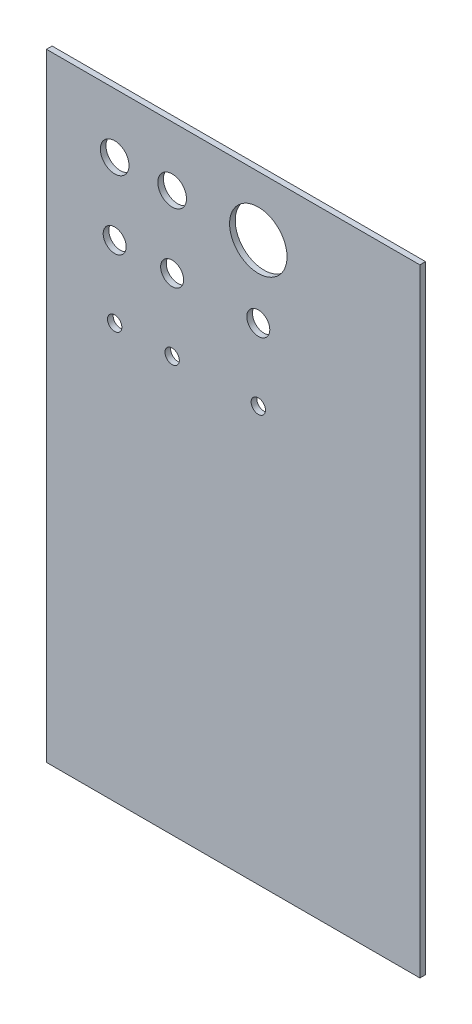
SolidWorks part; units mm, degrees
ref_plane "Front Plane" through (0, 0, 0) normal (0, 0, 1) x (1, 0, 0)
ref_plane "Top Plane" through (0, 0, 0) normal (0, 1, 0) x (1, 0, 0)
ref_plane "Right Plane" through (0, 0, 0) normal (1, 0, 0) x (0, 0, -1)
sketch "Sketch1" plane through (0, 0, 0) normal (0, 0, 1) x (1, 0, 0)
  circle B0 centre (1873.254, 4935.2365) radius 254
  line B1 (3302, 5461) -> (3302, 0)
  line B2 (0, 0) -> (0, 5461)
  line B3 (0, 5461) -> (3302, 5461)
  line B4 (3302, 0) -> (0, 0)
  circle B5 centre (603.254, 4935.2365) radius 127
  circle B6 centre (603.254, 4300.2365) radius 101.6
  circle B7 centre (603.254, 3665.2365) radius 63.5
  circle B8 centre (1111.254, 4935.2365) radius 127
  circle B9 centre (1111.254, 4300.2365) radius 101.6
  circle B10 centre (1111.254, 3665.2365) radius 63.5
  circle B11 centre (1873.254, 4300.2365) radius 101.6
  circle B12 centre (1873.254, 3665.2365) radius 63.5
sketch_block_instance "support-1"
sketch_block "support"
extrude "Boss-Extrude1" add sketch "Sketch1" along normal blind 50
scale "Scale1" scale about centroid uniform scaling yes scale factor 0.04
